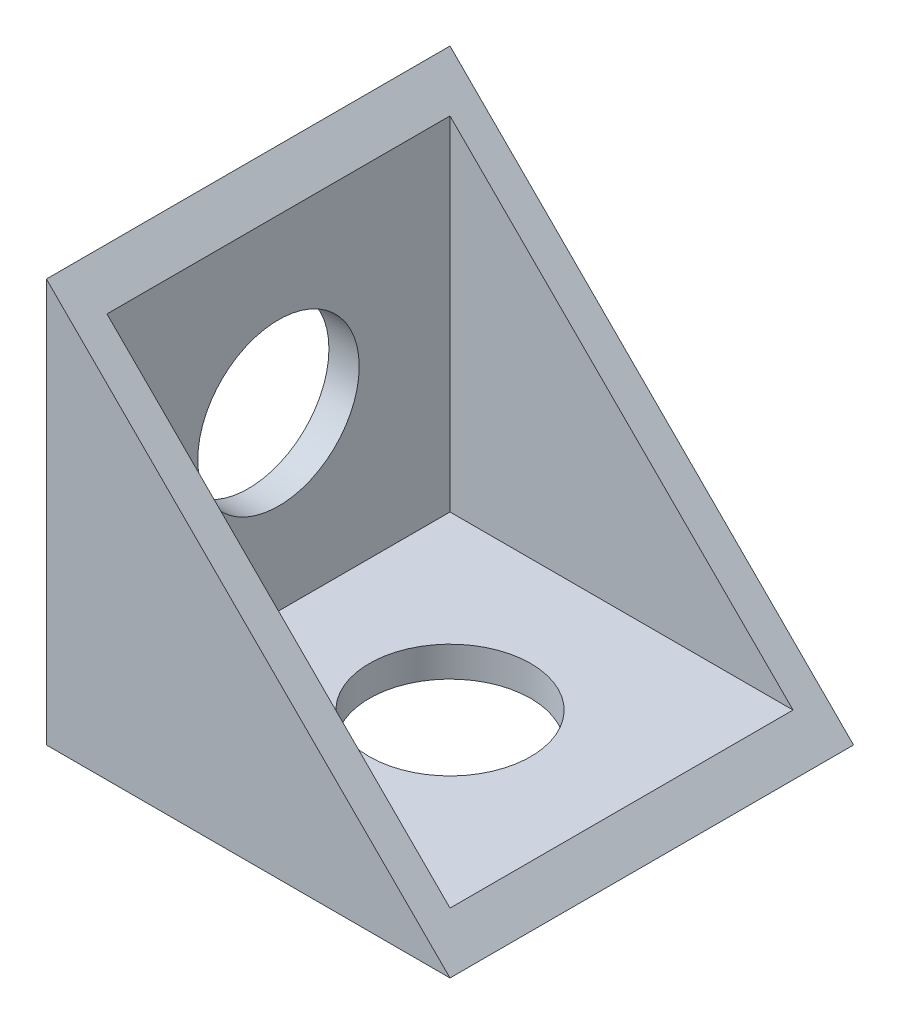
SolidWorks part; units mm, degrees
ref_plane "Front Plane" through (0, 0, 0) normal (0, 0, 1) x (1, 0, 0)
ref_plane "Top Plane" through (0, 0, 0) normal (0, 1, 0) x (1, 0, 0)
ref_plane "Right Plane" through (0, 0, 0) normal (1, 0, 0) x (0, 0, -1)
sketch "Sketch1" plane through (0, 0, 0) normal (0, 0, 1) x (1, 0, 0)
  line L3 (-10, 0) -> (10, 0)
  line L4 (10, 0) -> (-10, 20)
  line L5 (-10, 20) -> (-10, 0)
  line L6 (-10, 0) -> (0, 10) construction
  dimension "D1" = 20
  dimension "D2" = 20
  dimension "D3" = 0
  dimension "D4" = 10
  dimension "D5" = 45
extrude "Boss-Extrude1" add sketch "Sketch1" along normal mid plane 20
sketch "Sketch3" plane through (0, 0, 0) normal (0, 1, 0) x (1, 0, 0)
  circle A0 centre (0, 0) radius 4
  dimension "D1" = 8
extrude "Cut-Extrude1" cut sketch "Sketch3" along normal blind 20
sketch "Sketch4" plane through (0, 0, 0) normal (1, 0, 0) x (0, 0, -1)
  circle A0 centre (0, 10) radius 4
  dimension "D1" = 8
extrude "Cut-Extrude2" cut sketch "Sketch4" against normal mid plane 20
sketch "Sketch5" plane through (0, 0, 0) normal (1, 0, 0) x (0, 0, -1)
  line L0 (-10, 20) -> (10, 20) construction
  line L1 (-8.5, 20) -> (8.5, 20)
  line L2 (-8.5, 20) -> (-8.5, 1.5)
  line L3 (-8.5, 1.5) -> (8.5, 1.5)
  line L4 (8.5, 20) -> (8.5, 1.5)
  line L5 (-10, 0) -> (-10, 20) construction
  line L6 (10, 0) -> (10, 20) construction
  line L7 (11, 0) -> (-11, 0) construction
  dimension "D1" = 1.5
  dimension "D2" = 1.5
  dimension "D3" = 1.5
extrude "Cut-Extrude3" cut sketch "Sketch5" against normal blind 8.5 and the other way blind 10
